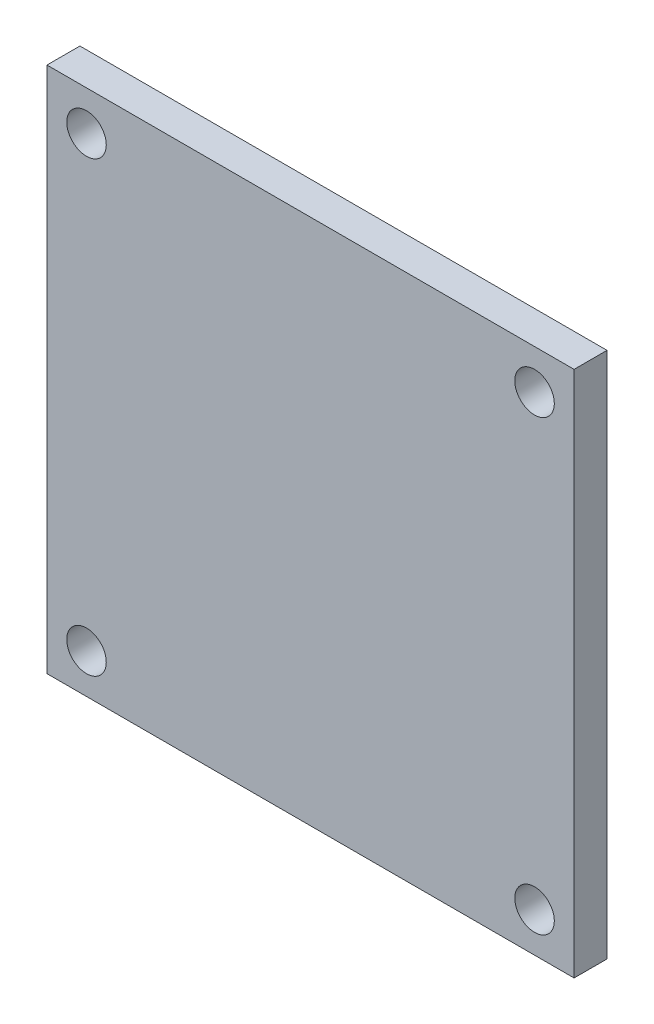
SolidWorks part; units mm, degrees
ref_plane "Front Plane" through (0, 0, 0) normal (0, 0, 1) x (1, 0, 0)
ref_plane "Top Plane" through (0, 0, 0) normal (0, 1, 0) x (1, 0, 0)
ref_plane "Right Plane" through (0, 0, 0) normal (1, 0, 0) x (0, 0, -1)
sketch "Sketch1" plane through (0, 0, 0) normal (0, 0, 1) x (1, 0, 0)
  line L1 (0, 0) -> (40, 0)
  line L2 (0, 0) -> (0, 40)
  line L3 (0, 40) -> (40, 40)
  line L4 (40, 0) -> (40, 40)
  dimension "D1" = 40
  dimension "D2" = 40
extrude "Boss-Extrude1" add sketch "Sketch1" along normal blind 2.5
sketch "Sketch2" plane through (0, 0, 2.5) normal (0, 0, 1) x (1, 0, 0)
  line L0 (40, 40) -> (0, 40) construction
  line L1 (0, 40) -> (0, 0) construction
  line L2 (0, 0) -> (40, 0) construction
  line L3 (40, 0) -> (40, 40) construction
  circle A0 centre (3, 37) radius 1.5
  circle A1 centre (37, 37) radius 1.5
  circle A2 centre (37, 3) radius 1.5
  circle A3 centre (3, 3) radius 1.5
  dimension "D5" = 3
  dimension "D6" = 3
  dimension "D7" = 3
  dimension "D8" = 3
  dimension "D12" = 3
  dimension "D1" = 3
  dimension "D2" = 3
  dimension "D3" = 3
  dimension "D4" = 3
  dimension "D9" = 3
  dimension "D10" = 3
  dimension "D11" = 3
extrude "Cut-Extrude1" cut sketch "Sketch2" against normal blind 2.5
